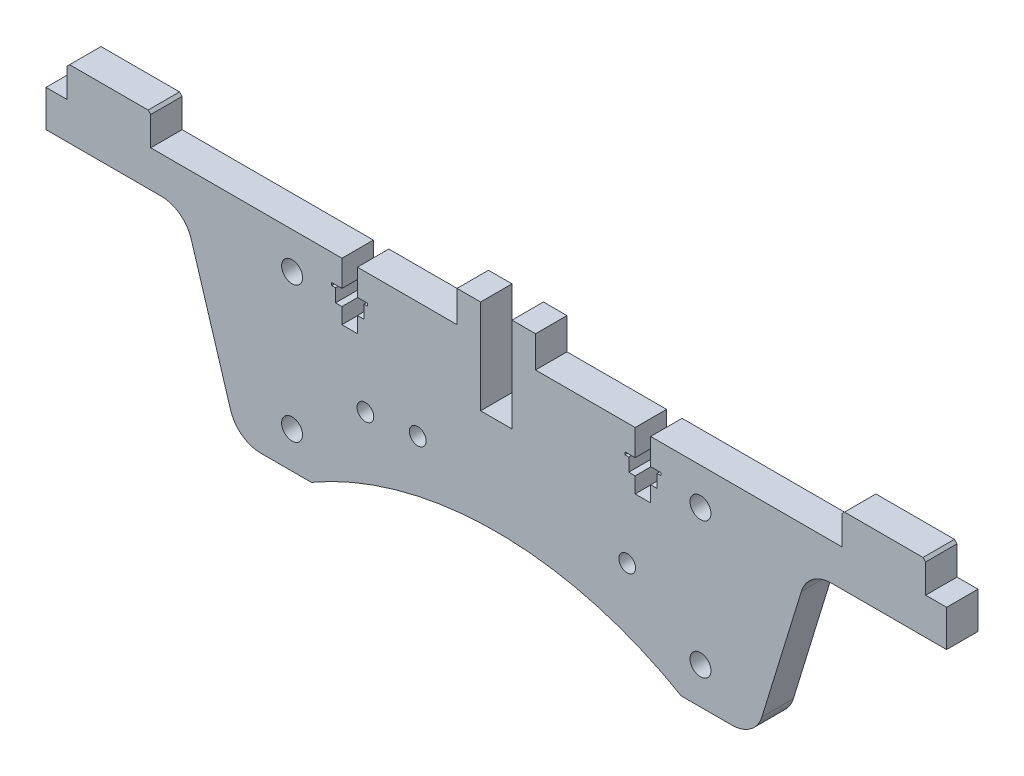
SolidWorks part; units mm, degrees
material "Oak"
ref_plane "Front Plane" through (0, 0, 0) normal (0, 0, 1) x (1, 0, 0)
ref_plane "Top Plane" through (0, 0, 0) normal (0, 1, 0) x (1, 0, 0)
ref_plane "Right Plane" through (0, 0, 0) normal (1, 0, 0) x (0, 0, -1)
sketch "Sketch1" plane through (0, 0, 0) normal (0, 0, 1) x (1, 0, 0)
  line L0 (0, -43.0686) -> (0, 56.6488) construction
  line L1 (-7.5, 20) -> (-66, 20)
  line L2 (49, 10.5) -> (65, 10.5) construction
  line L3 (49, 10.5) -> (49, -10.5) construction
  line L4 (49, -10.5) -> (65, -10.5) construction
  line L5 (65, 10.5) -> (65, -10.5) construction
  line L6 (66, 20) -> (66, 26)
  line L7 (66, 26) -> (82, 26)
  line L8 (86, 20) -> (86, 13)
  line L9 (-7.5, 20) -> (-7.5, 26)
  line L10 (35.3214, -20) -> (45, -20)
  line L11 (49, 10.5) -> (65, -10.5) construction
  line L12 (65, 10.5) -> (49, -10.5) construction
  line L13 (-65, 10.5) -> (-49, -10.5) construction
  line L14 (-49, 10.5) -> (-65, -10.5) construction
  line L15 (-65, 10.5) -> (-65, -10.5) construction
  line L16 (-49, -10.5) -> (-65, -10.5) construction
  line L17 (-49, 10.5) -> (-49, -10.5) construction
  line L18 (-49, 10.5) -> (-65, 10.5) construction
  line L19 (-7.5, 26) -> (-3, 26)
  line L20 (-64, 13) -> (-86, 13)
  line L21 (-82, 20) -> (-82, 26)
  line L22 (-86, 20) -> (-82, 20)
  line L23 (7.5, 20) -> (7.5, 26)
  line L24 (7.5, 26) -> (3, 26)
  line L25 (7.5, 20) -> (66, 20)
  line L26 (86, 20) -> (82, 20)
  line L27 (3, 26) -> (3, 8)
  line L28 (-57, 0) -> (57, 0) construction
  line L29 (3, 8) -> (-3, 8)
  line L30 (82, 20) -> (82, 26)
  line L31 (-86, 20) -> (-86, 13)
  line L32 (-66, 26) -> (-82, 26)
  line L33 (-35.3214, -20) -> (-45, -20)
  line L34 (-66, 20) -> (-66, 26)
  line L35 (-3, 26) -> (-3, 8)
  line L36 (-50.7358, -15.7609) -> (-58.2642, 8.7609)
  line L37 (50.7358, -15.7609) -> (58.2642, 8.7609)
  line L38 (64, 13) -> (86, 13)
  arc A0 (35.3214, -20) -> (-35.3214, -20) centre (0, -80.9132) ccw
  arc A1 (50.7358, -15.7609) -> (45, -20) centre (45, -14) cw
  arc A2 (58.2642, 8.7609) -> (64, 13) centre (64, 7) cw
  arc A6 (-58.2642, 8.7609) -> (-64, 13) centre (-64, 7) ccw
  arc A7 (-50.7358, -15.7609) -> (-45, -20) centre (-45, -14) ccw
  point P7 (-57, 0)
  point P9 (57, 0)
  point P20 (0, 0)
  point P24 (0, 40)
  point P25 (0, -10.5)
  point P27 (73.331, 42)
  point P30 (0, 40)
  point P31 (68.331, 20)
  point P32 (99.8, 42)
  point P38 (98.8347, 49.7973)
  point P54 (0, 8)
  dimension "D8" = 7
  dimension "D9" = 90
  dimension "D15" = 6
  dimension "D17" = 6
  dimension "D1" = 16
  dimension "D2" = 65
  dimension "D3" = 86
  dimension "D4" = 4
  dimension "D5" = 15
  dimension "D6" = 12
  dimension "D7" = 21
  dimension "D10" = 6
  dimension "D11" = 20
  dimension "D12" = 20
  dimension "D13" = 6
  dimension "D14" = 128
  dimension "D16" = 20
extrude "Boss-Extrude1" add sketch "Sketch1" along normal blind 6
sketch "Sketch2" plane through (0, 0, 6) normal (0, 0, 1) x (1, 0, 0)
  line L0 (0, 0) -> (0, -20) construction
  line L1 (-45, -20) -> (-35.3214, -20) construction
  line L2 (-25, -3.2) -> (25, -3.2) construction
  line L3 (0, 0) -> (0, -3.2) construction
  line L4 (66, 20) -> (7.5, 20) construction
  line L7 (31, -8) -> (31, 8) construction
  line L8 (31, -8) -> (47, -8) construction
  line L9 (31, 8) -> (47, 8) construction
  line L10 (47, -8) -> (47, 8) construction
  line L11 (31, -8) -> (47, 8) construction
  line L12 (31, 8) -> (47, -8) construction
  circle A0 centre (39, -13) radius 2
  circle A1 centre (39, 13) radius 2
  circle A2 centre (25, -3.2) radius 1.6
  circle A3 centre (-25, -3.2) radius 1.6
  point P7 (39, 0)
  dimension "D2" = 4
  dimension "D3" = 20
  dimension "D5" = 3.2
  dimension "D1" = 39
  dimension "D4" = 13
  dimension "D6" = 50
  dimension "D7" = 16
  dimension "D8" = 3.2
  dimension "D16" = 13
extrude "Cut-Extrude1" cut sketch "Sketch2" against normal through all
mirror "Mirror1" about plane through (0, 0, 0) normal (1, 0, 0) of "Cut-Extrude1"
chamfer "Chamfer1" distance 0.5 angle 45 4 edges at (66, 26, 3) (82, 26, 3) (-66, 26, 3) (-82, 26, 3)
sketch "Sketch4" plane through (0, 0, 6) normal (0, 0, 1) x (1, 0, 0)
  line L0 (0, 0) -> (0, 22.5154) construction
  line L1 (-28, 20) -> (-28, 9) construction
  line L2 (-7.5, 20) -> (-66, 20) construction
  line L3 (-29.48, 20) -> (-29.48, 15)
  line L4 (-29.48, 15) -> (-31.45, 15)
  line L5 (-31.45, 15) -> (-31.45, 14.5)
  line L6 (-31.45, 14.5) -> (-30.7, 14.5)
  line L7 (-30.7, 14.5) -> (-30.7, 12)
  line L8 (-30.7, 12) -> (-29.48, 12)
  line L9 (-29.48, 12) -> (-29.48, 9)
  line L10 (-29.48, 9) -> (-26.52, 9)
  line L11 (-26.52, 12) -> (-26.52, 9)
  line L12 (-25.3, 12) -> (-26.52, 12)
  line L13 (-25.3, 14.5) -> (-25.3, 12)
  line L14 (-24.55, 14.5) -> (-25.3, 14.5)
  line L15 (-24.55, 15) -> (-24.55, 14.5)
  line L16 (-26.52, 15) -> (-24.55, 15)
  line L17 (-26.52, 20) -> (-26.52, 15)
  line L18 (28, 20) -> (28, 9) construction
  line L19 (26.52, 20) -> (26.52, 15)
  line L20 (26.52, 15) -> (24.55, 15)
  line L21 (24.55, 15) -> (24.55, 14.5)
  line L22 (24.55, 14.5) -> (25.3, 14.5)
  line L23 (25.3, 14.5) -> (25.3, 12)
  line L24 (25.3, 12) -> (26.52, 12)
  line L25 (26.52, 12) -> (26.52, 9)
  line L26 (29.48, 9) -> (26.52, 9)
  line L27 (29.48, 12) -> (29.48, 9)
  line L28 (30.7, 12) -> (29.48, 12)
  line L29 (30.7, 14.5) -> (30.7, 12)
  line L30 (31.45, 14.5) -> (30.7, 14.5)
  line L31 (31.45, 15) -> (31.45, 14.5)
  line L32 (29.48, 15) -> (31.45, 15)
  line L33 (29.48, 20) -> (29.48, 15)
  line L34 (-29.48, 20) -> (-26.52, 20)
  line L35 (26.52, 20) -> (29.48, 20)
  dimension "D1" = 0.5
  dimension "D2" = 2.5
  dimension "D3" = 3
  dimension "D4" = 11
  dimension "D5" = 2.96
  dimension "D6" = 6.9
  dimension "D7" = 5.4
  dimension "D8" = 28
extrude "Cut-Extrude2" cut sketch "Sketch4" against normal through all
sketch "Sketch5" plane through (0, 0, 6) normal (0, 0, 1) x (1, 0, 0)
  circle A0 centre (-15, -2.2) radius 1.6
  circle A1 centre (-25, -3.2) radius 1.6 construction
  point P2 (-25, -3.2)
  dimension "D1" = 10
  dimension "D2" = 1
extrude "Cut-Extrude3" cut sketch "Sketch5" against normal through all
equation "\"bed-plate-thickness\"=6"
equation "\"D1@Boss-Extrude1\"=\"y-rib-thickness\""
equation "\"D10@Sketch1\"=\"bed-plate-thickness\""
equation "\"D13@Sketch1\"=\"y-cross-rib-thickness\""
equation "\"y-cross-rib-thickness\"=6"
equation "\"y-rib-thickness\"=6"
equation "\"x-plate-thickness\"=5"
equation "\"rod-diameter\"=12"
equation "\"t-nut-hole-diameter\"=3"
equation "\"y-plate-thickness\"=5"
equation "\"D8@Sketch2\"=9-(11.6/2)"
